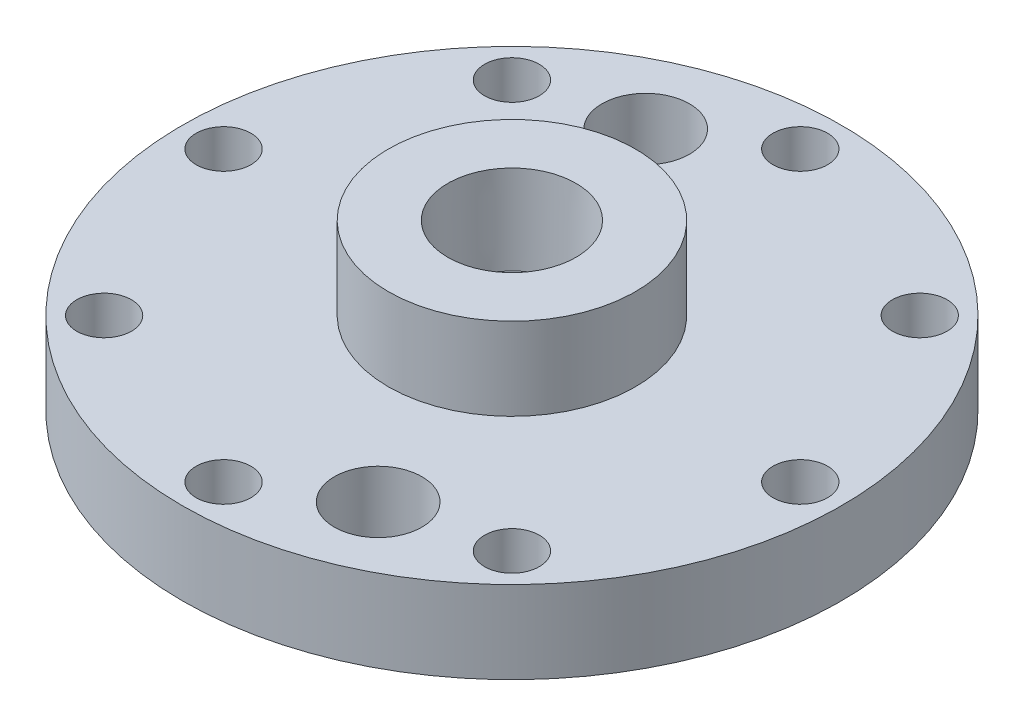
SolidWorks part; units mm, degrees
ref_plane "Front Plane" through (0, 0, 0) normal (0, 0, 1) x (1, 0, 0)
ref_plane "Top Plane" through (0, 0, 0) normal (0, 1, 0) x (1, 0, 0)
ref_plane "Right Plane" through (0, 0, 0) normal (1, 0, 0) x (0, 0, -1)
sketch "Sketch1" plane through (0, 0, 0) normal (0, 0, 1) x (1, 0, 0)
  line L0 (-19.431, 0) -> (-50.8, 0)
  line L1 (-50.8, 0) -> (-50.8, 12.7)
  line L2 (-50.8, 12.7) -> (-19.05, 12.7)
  line L3 (0, 25.4) -> (0, 0)
  line L4 (-19.431, 0) -> (-19.431, 2.54)
  line L5 (-19.431, 2.54) -> (-15.875, 2.54)
  line L6 (-15.875, 2.54) -> (-15.875, 0)
  line L7 (-15.875, 0) -> (0, 0)
  line L8 (0, 25.4) -> (-19.05, 25.4)
  line L9 (-19.05, 25.4) -> (-19.05, 12.7)
  dimension "D1" = 50.8
  dimension "D2" = 12.7
  dimension "D3" = 19.05
  dimension "D4" = 3.556
  dimension "D5" = 2.54
  dimension "D6" = 12.7
  dimension "D7" = 15.875
revolve "Revolve1" add sketch "Sketch1" angle 360 about L3
hole_wizard "1/2 NPT Tapped Hole1" positions "Sketch2" profile "Sketch4" size "1/2" standard "ANSI Inch" end condition through all
sketch "Sketch2" plane through (0, 25.4, 0) normal (0, 1, 0) x (1, 0, 0)
  point P0 (0, 0)
sketch "Sketch4" plane through (0, 25.4, 0) normal (1, 0, 0) x (0, 0, 1)
  line L0 (0, 0) -> (0, 25.4)
  line L1 (0, 25.4) -> (8.9281, 25.4)
  line L2 (-9.4797, 13.462) -> (-9.8828, 0) construction
  line L3 (8.9281, 25.4) -> (8.9281, 13.462)
  line L4 (8.9281, 13.462) -> (9.4797, 13.462)
  line L5 (9.4797, 13.462) -> (9.8828, 0)
  line L7 (9.8828, 0) -> (0, 0)
  line L8 (0, -6.35) -> (0, 107.95) construction
  line L11 (-8.9281, 13.462) -> (-9.4797, 13.462) construction
  dimension "Thru Tap Drill Dia." = 17.8562
  dimension "Thru Tap Drill Depth" = 25.4
  dimension "Thread Dia." = 19.7656
  dimension "Thread Angle" = 3.43
  dimension "Thread Depth" = 13.462
cosmetic thread "Hole Thread1" parameters "D1"=13.462, "D2"=21.3288
hole_wizard "5/16 Clearance Hole1" positions "Sketch5" profile "Sketch6" hole size "5/16" standard "ANSI Inch" end condition through all
sketch "Sketch5" plane through (0, 12.7, 0) normal (0, 1, 0) x (1, 0, 0)
  point P0 (44.45, 0)
  dimension "D1" = 44.45
sketch "Sketch6" plane through (44.45, 12.7, 0) normal (1, 0, 0) x (0, 0, 1)
  line L0 (0, 0) -> (0, 12.7)
  line L1 (0, 12.7) -> (4.2164, 12.7)
  line L2 (4.2164, 12.7) -> (4.2164, 0)
  line L5 (4.2164, 0) -> (0, 0)
  line L11 (0, -6.35) -> (0, 107.95) construction
  dimension "Thru Hole Dia." = 8.4328
  dimension "Thru Hole Depth" = 12.7
pattern_circular "CirPattern1" count 8 over 360 about axis through (0, 0, 0) along (0, 1, 0) of "5/16 Clearance Hole1"
hole_wizard "1/2 Clearance Hole1" positions "Sketch7" profile "Sketch8" hole size "1/2" standard "ANSI Inch" end condition through all
sketch "Sketch7" plane through (0, 12.7, 0) normal (0, 1, 0) x (1, 0, 0)
  line L0 (0, 0) -> (-14.5802, 35.1998) construction
  line L2 (0, 0) -> (0, 30.2547) construction
  point P0 (-14.5802, 35.1998)
  dimension "D1" = 22.5
  dimension "D2" = 38.1
sketch "Sketch8" plane through (-14.5802, 12.7, -35.1998) normal (1, 0, 0) x (0, 0, 1)
  line L0 (0, 0) -> (0, 12.7)
  line L1 (0, 12.7) -> (6.7462, 12.7)
  line L2 (6.7462, 12.7) -> (6.7462, 0)
  line L5 (6.7462, 0) -> (0, 0)
  line L11 (0, -6.35) -> (0, 107.95) construction
  dimension "Thru Hole Dia." = 13.4925
  dimension "Thru Hole Depth" = 12.7
pattern_circular "CirPattern2" count 2 over 360 about axis through (0, 0, 0) along (0, 1, 0) of "1/2 Clearance Hole1"
